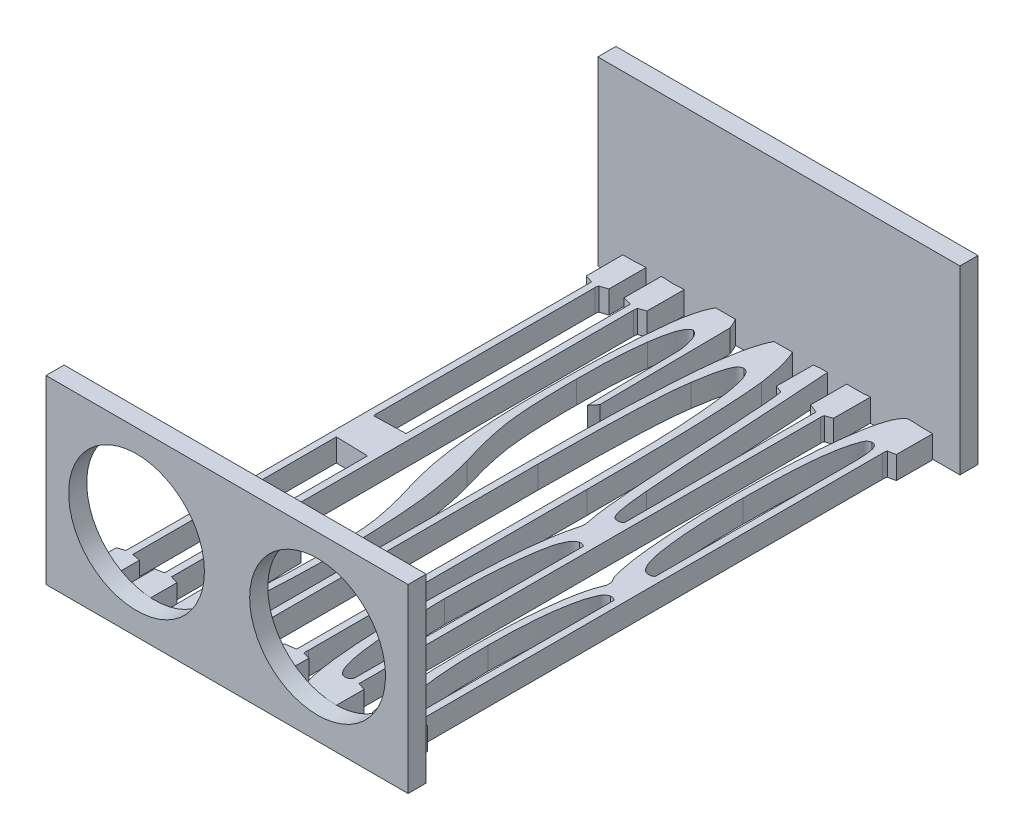
SolidWorks part; units mm, degrees
ref_plane "Front Plane" through (0, 0, 0) normal (0, 0, 1) x (1, 0, 0)
ref_plane "Top Plane" through (0, 0, 0) normal (0, 1, 0) x (1, 0, 0)
ref_plane "Right Plane" through (0, 0, 0) normal (1, 0, 0) x (0, 0, -1)
sketch "Sketch1" plane through (0, 0, 0) normal (0, 1, 0) x (1, 0, 0)
  line L1 (25.4, 1.27) -> (-25.4, 1.27)
  line L2 (25.4, 1.27) -> (25.4, -1.27)
  line L3 (25.4, -1.27) -> (-25.4, -1.27)
  line L4 (-25.4, 1.27) -> (-25.4, -1.27)
  line L5 (25.4, 1.27) -> (-25.4, -1.27) construction
  line L6 (25.4, -1.27) -> (-25.4, 1.27) construction
  point P0 (0, 0)
  dimension "D1" = 50.8
  dimension "D2" = 2.54
extrude "Boss-Extrude1" add sketch "Sketch1" along normal blind 25.4
sketch "Sketch4" plane through (0, 0, 0) normal (0, -1, 0) x (1, 0, 0)
  line L0 (-25.4, 1.27) -> (25.4, 1.27) construction
  text T0 "BRUSH" font "Chaparral Pro" height 76.2
extrude "Boss-Extrude3" add sketch "Sketch4" against normal blind 3.175
sketch "Sketch6" plane through (0, 0, 77.419) normal (0, 0, 1) x (1, 0, 0)
  line L1 (-25.4, 0) -> (25.4, 0)
  line L2 (-25.4, 0) -> (-25.4, 25.4)
  line L3 (-25.4, 25.4) -> (25.4, 25.4)
  line L4 (25.4, 0) -> (25.4, 25.4)
extrude "Boss-Extrude8" add sketch "Sketch6" against normal blind 1.27
sketch "Sketch7" plane through (0, 0, 77.419) normal (0, 0, 1) x (1, 0, 0)
  line L1 (-25.4, 0) -> (25.4, 0)
  line L2 (-25.4, 0) -> (-25.4, 25.4)
  line L3 (-25.4, 25.4) -> (25.4, 25.4)
  line L4 (25.4, 0) -> (25.4, 25.4)
extrude "Boss-Extrude9" add sketch "Sketch7" along normal blind 1.27
sketch "Sketch8" plane through (0, 0, 78.689) normal (0, 0, 1) x (1, 0, 0)
  line L0 (25.4, 25.4) -> (-25.4, 25.4) construction
  line L1 (-25.4, 25.4) -> (-25.4, 0) construction
  circle A0 centre (-12.7, 12.7) radius 9.525
  dimension "D1" = 19.05
  dimension "D2" = 12.7
  dimension "D3" = 12.7
extrude "Cut-Extrude1" cut sketch "Sketch8" against normal blind 2.54
mirror "Mirror1" about plane through (0, 0, 0) normal (1, 0, 0) of "Cut-Extrude1"
